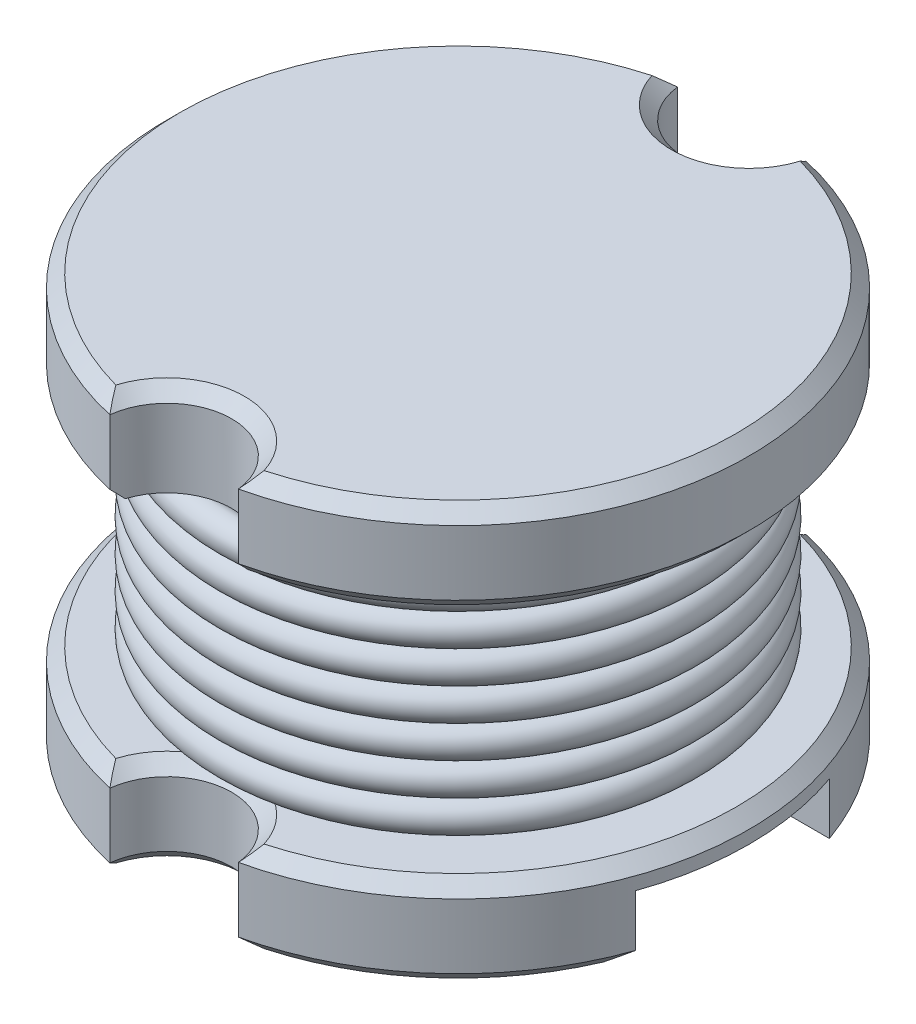
SolidWorks part; units mm, degrees
ref_plane "Front Plane" through (0, 0, 0) normal (0, 0, 1) x (1, 0, 0)
ref_plane "Top Plane" through (0, 0, 0) normal (0, 1, 0) x (1, 0, 0)
ref_plane "Right Plane" through (0, 0, 0) normal (1, 0, 0) x (0, 0, -1)
sketch "Sketch1" plane through (0, 0, 0) normal (0, 1, 0) x (1, 0, 0)
  circle A0 centre (0, 0) radius 2.25
  dimension "D1" = 4.5
extrude "Boss-Extrude1" add sketch "Sketch1" along normal blind 0.7
sketch "Sketch2" plane through (0, 0.7, 0) normal (0, 1, 0) x (1, 0, 0)
  circle A0 centre (0, 0) radius 1.5
  dimension "D1" = 3
extrude "Boss-Extrude2" add sketch "Sketch2" along normal blind 1.8
sketch "Sketch3" plane through (0, 2.5, 0) normal (0, 1, 0) x (1, 0, 0)
  circle A0 centre (0, 0) radius 2.25
  dimension "D1" = 4.5
extrude "Boss-Extrude3" add sketch "Sketch3" along normal blind 0.7
sketch "Sketch5" plane through (0, 3.2, 0) normal (0, 1, 0) x (1, 0, 0)
  circle A0 centre (0, -2.25) radius 0.5
  circle A1 centre (0, 0) radius 2.25 construction
  circle A2 centre (0, 2.25) radius 0.5
  dimension "D1" = 1
  dimension "D2" = 1
extrude "Cut-Extrude2" cut sketch "Sketch5" against normal up to surface (3.2 mm away) up to face at (0, 0, 2.25)
ref_plane "Plane1" through (0, 0.825, 0) normal (0, 1, 0) x (1, 0, 0)
sketch "Sketch6" plane through (0, 0.825, 0) normal (0, 1, 0) x (1, 0, 0)
  circle A0 centre (0, 0) radius 1.75
  dimension "D1" = 3.5
sweep "Sweep1" add path "Sketch6" circular profile diameter 0.25 parameters "D3"=0.25
pattern_linear "LPattern4" count 7 spacing 0.25 along (0, 1, 0) of "Sweep1"
sketch "Sketch87" plane through (0, 0, 0) normal (0, -1, 0) x (1, 0, 0)
  line L1 (5.2903, 0.75) -> (-5.2903, 0.75)
  line L2 (5.2903, 0.75) -> (5.2903, -0.75)
  line L3 (5.2903, -0.75) -> (-5.2903, -0.75)
  line L4 (-5.2903, 0.75) -> (-5.2903, -0.75)
  line L5 (5.2903, 0.75) -> (-5.2903, -0.75) construction
  line L6 (5.2903, -0.75) -> (-5.2903, 0.75) construction
  point P0 (0, 0)
  dimension "D1" = 1.5
extrude "Cut-Extrude3" cut sketch "Sketch87" against normal blind 0.5
chamfer "Chamfer1" distance 0.1 angle 45 19 edges at (0, 0.7, 1.5) (-2.25, 0.7, 0) (2.25, 0.7, 0) (0, 0.7, 1.75) (0, 0.7, -1.75) (-2.25, 2.5, 0) (2.25, 2.5, 0) (0, 0, 1.75) (-1.4951, 0, 1.6814) (1.4951, 0, 1.6814) (0, 0, 0.75) (0, 0, -1.75) (-1.4951, 0, -1.6814) (1.4951, 0, -1.6814) (0, 0, -0.75) (-2.25, 3.2, 0) (2.25, 3.2, 0) (0, 3.2, 1.75) (0, 3.2, -1.75)
